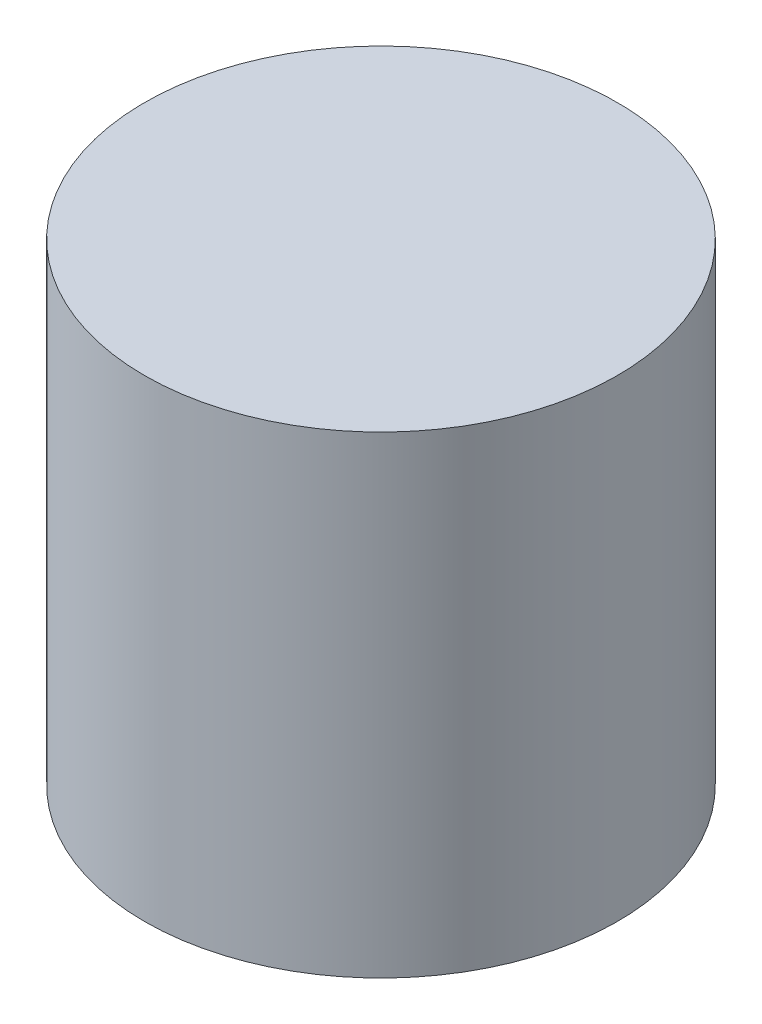
SolidWorks part; units mm, degrees
ref_plane "Front Plane" through (0, 0, 0) normal (0, 0, 1) x (1, 0, 0)
ref_plane "Top Plane" through (0, 0, 0) normal (0, 1, 0) x (1, 0, 0)
ref_plane "Right Plane" through (0, 0, 0) normal (1, 0, 0) x (0, 0, -1)
sketch "Sketch1" plane through (0, 0, 0) normal (0, 1, 0) x (1, 0, 0)
  circle A0 centre (0, 0) radius 3
  dimension "D1" = 6
extrude "Boss-Extrude1" add sketch "Sketch1" along normal blind 6
